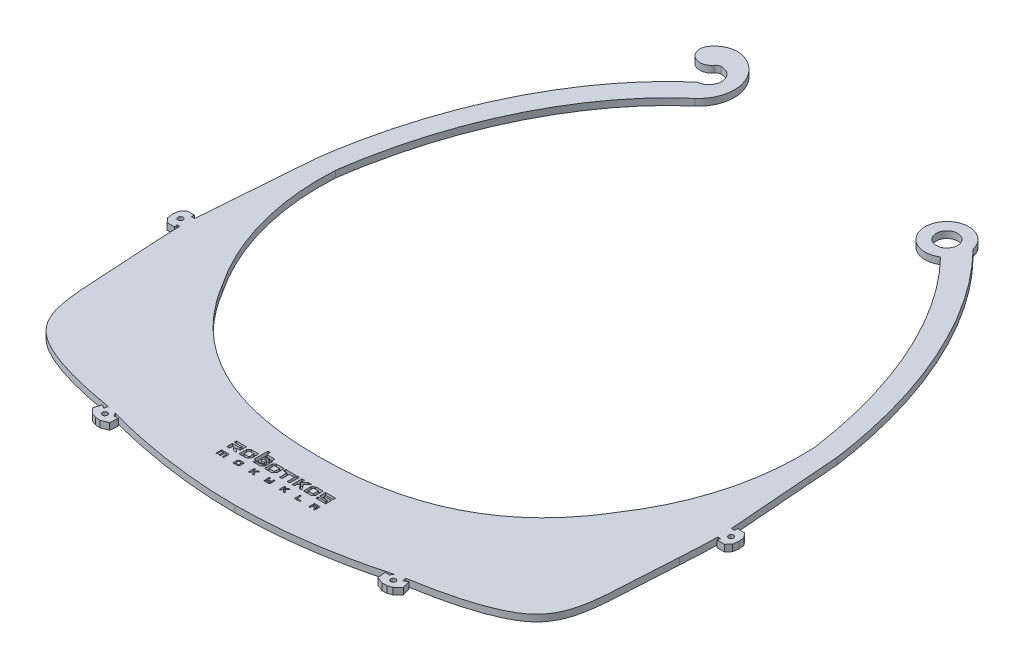
SolidWorks part; units mm, degrees
ref_plane "Front Plane" through (0, 0, 0) normal (0, 0, 1) x (1, 0, 0)
ref_plane "Top Plane" through (0, 0, 0) normal (0, 1, 0) x (1, 0, 0)
ref_plane "Right Plane" through (0, 0, 0) normal (1, 0, 0) x (0, 0, -1)
sketch "Sketch1" plane through (0, 0, 0) normal (0, 1, 0) x (1, 0, 0)
  line L0 (-56.7342, 4649.685) -> (-54.3432, 4649.8666)
  line L1 (-54.3432, 4649.8666) -> (-51.9673, 4650.1279)
  line L2 (-51.9673, 4650.1279) -> (-49.6128, 4650.4904)
  line L3 (-49.6128, 4650.4904) -> (-47.2873, 4650.9763)
  line L4 (-47.2873, 4650.9763) -> (-45.0028, 4651.606)
  line L5 (-45.0028, 4651.606) -> (-42.7754, 4652.393)
  line L6 (-42.7754, 4652.393) -> (-40.6236, 4653.3398)
  line L7 (-40.6236, 4653.3398) -> (-38.5569, 4654.4471)
  line L8 (-38.5569, 4654.4471) -> (-36.5628, 4655.7048)
  line L9 (-36.5628, 4655.7048) -> (-34.628, 4657.0886)
  line L10 (-34.628, 4657.0886) -> (-32.7572, 4658.5809)
  line L11 (-32.7572, 4658.5809) -> (-31.8781, 4659.3559)
  line L12 (-31.8781, 4659.3559) -> (-31.0378, 4660.1663)
  line L13 (-31.0378, 4660.1663) -> (-30.2434, 4661.0133)
  line L14 (-30.2434, 4661.0133) -> (-29.4929, 4661.8977)
  line L15 (-29.4929, 4661.8977) -> (-28.0377, 4663.8002)
  line L16 (-28.0377, 4663.8002) -> (-26.6418, 4665.7643)
  line L17 (-26.6418, 4665.7643) -> (-25.2842, 4667.7433)
  line L18 (-25.2842, 4667.7433) -> (-24.5616, 4668.7671)
  line L19 (-24.5616, 4668.7671) -> (-24.1207, 4669.3049)
  line L20 (-24.1207, 4669.3049) -> (-23.6287, 4669.8041)
  line L21 (-23.6287, 4669.8041) -> (-22.6527, 4670.6453)
  line L22 (-22.6527, 4670.6453) -> (-21.6624, 4671.4168)
  line L23 (-21.6624, 4671.4168) -> (-19.7154, 4672.8766)
  line L24 (-19.7154, 4672.8766) -> (-18.7888, 4673.6051)
  line L25 (-18.7888, 4673.6051) -> (-17.9151, 4674.3646)
  line L26 (-17.9151, 4674.3646) -> (-17.0961, 4675.1711)
  line L27 (-17.0961, 4675.1711) -> (-16.3332, 4676.0235)
  line L28 (-16.3332, 4676.0235) -> (-14.888, 4677.8872)
  line L29 (-14.888, 4677.8872) -> (-14.2651, 4678.8282)
  line L30 (-14.2651, 4678.8282) -> (-13.7395, 4679.8092)
  line L31 (-13.7395, 4679.8092) -> (-13.3157, 4680.8364)
  line L32 (-13.3157, 4680.8364) -> (-12.9921, 4681.9053)
  line L33 (-12.9921, 4681.9053) -> (-12.765, 4683.0137)
  line L34 (-12.765, 4683.0137) -> (-12.6116, 4684.156)
  line L35 (-12.6116, 4684.156) -> (-12.4221, 4686.5439)
  line L36 (-12.4221, 4686.5439) -> (-12.3049, 4688.9547)
  line L37 (-12.3049, 4688.9547) -> (-12.23, 4691.3606)
  line L38 (-12.23, 4691.3606) -> (-12.2173, 4693.7469)
  line L39 (-12.2173, 4693.7469) -> (-12.2979, 4696.128)
  line L40 (-12.2979, 4696.128) -> (-12.4621, 4698.525)
  line L41 (-12.4621, 4698.525) -> (-12.9016, 4703.3562)
  line L42 (-12.9016, 4703.3562) -> (-13.1725, 4705.7323)
  line L43 (-13.1725, 4705.7323) -> (-13.359, 4706.8497)
  line L44 (-13.359, 4706.8497) -> (-13.6464, 4707.8976)
  line L45 (-13.6464, 4707.8976) -> (-13.8331, 4708.3435)
  line L46 (-13.8331, 4708.3435) -> (-14.0727, 4708.7863)
  line L47 (-14.0727, 4708.7863) -> (-14.3603, 4709.2104)
  line L48 (-14.3603, 4709.2104) -> (-14.6922, 4709.6118)
  line L49 (-14.6922, 4709.6118) -> (-15.5352, 4710.4427)
  line L50 (-15.5352, 4710.4427) -> (-16.4733, 4711.2489)
  line L51 (-16.4733, 4711.2489) -> (-18.3969, 4712.8768)
  line L52 (-18.3969, 4712.8768) -> (-19.3317, 4713.7593)
  line L53 (-19.3317, 4713.7593) -> (-19.7964, 4714.2738)
  line L54 (-19.7964, 4714.2738) -> (-20.226, 4714.8564)
  line L55 (-20.226, 4714.8564) -> (-20.8491, 4716.0227)
  line L56 (-20.8491, 4716.0227) -> (-21.3607, 4717.2182)
  line L57 (-21.3607, 4717.2182) -> (-22.2565, 4719.6128)
  line L58 (-22.2565, 4719.6128) -> (-23.9365, 4724.4003)
  line L59 (-23.9365, 4724.4003) -> (-24.8142, 4726.6925)
  line L60 (-24.8142, 4726.6925) -> (-25.7235, 4728.951)
  line L61 (-25.7235, 4728.951) -> (-29.4192, 4737.978)
  line L62 (-29.4192, 4737.978) -> (-31.3112, 4742.476)
  line L63 (-31.3112, 4742.476) -> (-32.3108, 4744.6883)
  line L64 (-32.3108, 4744.6883) -> (-33.3653, 4746.8748)
  line L65 (-33.3653, 4746.8748) -> (-34.484, 4749.0197)
  line L66 (-34.484, 4749.0197) -> (-35.6822, 4751.1089)
  line L67 (-35.6822, 4751.1089) -> (-36.9697, 4753.1376)
  line L68 (-36.9697, 4753.1376) -> (-38.335, 4755.1176)
  line L69 (-38.335, 4755.1176) -> (-39.7566, 4757.0561)
  line L70 (-39.7566, 4757.0561) -> (-41.2239, 4758.9538)
  line L71 (-41.2239, 4758.9538) -> (-44.2837, 4762.6862)
  line L72 (-44.2837, 4762.6862) -> (-45.0093, 4763.5782)
  line L73 (-45.7102, 4766.0333) -> (-45.6003, 4766.895)
  line L74 (-44.3387, 4767.2717) -> (-41.5099, 4763.9631)
  line L75 (-41.5099, 4763.9631) -> (-39.7615, 4761.7893)
  line L76 (-39.7615, 4761.7893) -> (-36.1552, 4757.1077)
  line L77 (-36.1552, 4757.1077) -> (-34.4224, 4754.6956)
  line L78 (-34.4224, 4754.6956) -> (-32.818, 4752.1875)
  line L79 (-32.818, 4752.1875) -> (-31.4001, 4749.5854)
  line L80 (-31.4001, 4749.5854) -> (-30.1172, 4746.945)
  line L81 (-30.1172, 4746.945) -> (-27.7453, 4741.6402)
  line L82 (-27.7453, 4741.6402) -> (-25.4835, 4736.2816)
  line L83 (-25.4835, 4736.2816) -> (-23.2904, 4730.8724)
  line L84 (-23.2904, 4730.8724) -> (-21.1708, 4725.4153)
  line L85 (-21.1708, 4725.4153) -> (-19.1018, 4719.943)
  line L86 (-19.1018, 4719.943) -> (-18.1004, 4717.2034)
  line L87 (-18.1004, 4717.2034) -> (-17.875, 4716.5966)
  line L88 (-17.875, 4716.5966) -> (-17.6236, 4716.1359)
  line L89 (-17.6236, 4716.1359) -> (-17.2675, 4715.7336)
  line L90 (-17.2675, 4715.7336) -> (-16.7845, 4715.2999)
  line L91 (-16.7845, 4715.2999) -> (-14.566, 4713.4273)
  line L92 (-14.566, 4713.4273) -> (-13.4359, 4712.453)
  line L93 (-13.4359, 4712.453) -> (-12.2875, 4711.3506)
  line L94 (-12.2875, 4711.3506) -> (-11.7288, 4710.5494)
  line L95 (-11.7288, 4710.5494) -> (-11.4049, 4709.6505)
  line L96 (-11.4049, 4709.6505) -> (-11.1035, 4708.0976)
  line L97 (-11.1035, 4708.0976) -> (-10.7039, 4705.1867)
  line L98 (-10.7039, 4705.1867) -> (-10.3782, 4702.2301)
  line L99 (-10.3782, 4702.2301) -> (-10.1381, 4699.312)
  line L100 (-10.1381, 4699.312) -> (-9.9526, 4696.4059)
  line L101 (-9.9526, 4696.4059) -> (-9.8234, 4693.4642)
  line L102 (-9.8234, 4693.4642) -> (-9.7818, 4690.5097)
  line L103 (-9.7818, 4690.5097) -> (-9.8395, 4687.5651)
  line L104 (-9.8395, 4687.5651) -> (-10.1467, 4681.8499)
  line L105 (-10.2187, 4680.4106) -> (-10.5778, 4674.8324)
  line L106 (-10.5778, 4674.8324) -> (-10.9255, 4669.1921)
  line L107 (-10.9255, 4669.1921) -> (-11.1085, 4666.3239)
  line L108 (-11.1085, 4666.3239) -> (-11.3672, 4663.3976)
  line L109 (-11.3672, 4663.3976) -> (-11.5954, 4661.8877)
  line L110 (-11.5954, 4661.8877) -> (-11.9481, 4660.3817)
  line L111 (-11.9481, 4660.3817) -> (-12.469, 4658.9063)
  line L112 (-12.469, 4658.9063) -> (-13.1768, 4657.5086)
  line L113 (-13.1768, 4657.5086) -> (-14.0475, 4656.2056)
  line L114 (-14.0475, 4656.2056) -> (-15.0678, 4655.0233)
  line L115 (-15.0678, 4655.0233) -> (-15.6664, 4654.4674)
  line L116 (-15.6664, 4654.4674) -> (-16.3022, 4653.9611)
  line L117 (-16.3022, 4653.9611) -> (-17.6055, 4653.1269)
  line L118 (-17.6055, 4653.1269) -> (-18.9712, 4652.4383)
  line L119 (-18.9712, 4652.4383) -> (-20.3502, 4651.8561)
  line L120 (-20.3502, 4651.8561) -> (-21.7405, 4651.3486)
  line L121 (-21.7405, 4651.3486) -> (-23.1491, 4650.8937)
  line L122 (-23.1491, 4650.8937) -> (-25.9685, 4650.1281)
  line L123 (-25.9685, 4650.1281) -> (-28.8127, 4649.495)
  line L124 (-28.8127, 4649.495) -> (-34.3611, 4648.4388)
  line L125 (-35.7786, 4648.1905) -> (-42.1243, 4647.1501)
  line L126 (-42.1243, 4647.1501) -> (-45.3893, 4646.7207)
  line L127 (-45.3893, 4646.7207) -> (-48.6635, 4646.3827)
  line L128 (-48.6635, 4646.3827) -> (-55.1892, 4645.922)
  line L129 (-55.1892, 4645.922) -> (-61.7354, 4645.5886)
  line L130 (-61.7354, 4645.5886) -> (-63.9666, 4645.5453)
  line L131 (-63.9667, 4649.4865) -> (-59.1315, 4649.5688)
  line L132 (-59.1315, 4649.5688) -> (-56.7342, 4649.685)
  line L133 (-9.7721, 4681.8294) -> (-9.752, 4682.186)
  line L134 (-9.752, 4682.186) -> (-9.3693, 4682.5229)
  line L135 (-9.3693, 4682.5229) -> (-8.649, 4682.4768)
  line L136 (-8.649, 4682.4768) -> (-7.9775, 4681.713)
  line L137 (-7.9775, 4681.713) -> (-8.2411, 4680.2884)
  line L138 (-8.2411, 4680.2884) -> (-9.0059, 4679.6162)
  line L139 (-9.0059, 4679.6162) -> (-9.5491, 4679.6473)
  line L140 (-9.5491, 4679.6473) -> (-9.8867, 4680.0303)
  line L141 (-9.8867, 4680.0303) -> (-9.8664, 4680.3889)
  line L142 (-9.7721, 4681.8294) -> (-9.752, 4682.186)
  line L151 (-34.2991, 4648.0806) -> (-33.9447, 4648.1421)
  line L152 (-33.9447, 4648.1421) -> (-33.5285, 4647.8485)
  line L153 (-33.5285, 4647.8485) -> (-33.4056, 4647.1395)
  line L154 (-33.4056, 4647.1395) -> (-33.9931, 4646.3074)
  line L155 (-33.9931, 4646.3074) -> (-35.4108, 4646.0612)
  line L156 (-35.4108, 4646.0612) -> (-36.2441, 4646.6493)
  line L157 (-36.2441, 4646.6493) -> (-36.3669, 4647.358)
  line L158 (-36.3669, 4647.358) -> (-36.0733, 4647.7743)
  line L159 (-36.0733, 4647.7743) -> (-35.7187, 4647.8357)
  line L160 (-10.1467, 4681.8499) -> (-9.7721, 4681.8294)
  line L161 (-34.3611, 4648.4388) -> (-34.2991, 4648.0806)
  line L162 (-35.7786, 4648.1905) -> (-35.7187, 4647.8357)
  line L163 (-9.8664, 4680.3889) -> (-10.2187, 4680.4106)
  line L165 (-118.1813, 4682.186) -> (-118.5641, 4682.5226)
  line L166 (-118.5641, 4682.5226) -> (-119.2843, 4682.4768)
  line L167 (-119.2843, 4682.4768) -> (-119.9558, 4681.7128)
  line L168 (-119.9558, 4681.7128) -> (-119.8643, 4680.2786)
  line L169 (-119.8643, 4680.2786) -> (-119.0995, 4679.6064)
  line L170 (-119.0995, 4679.6064) -> (-118.3843, 4679.6471)
  line L171 (-118.3843, 4679.6471) -> (-118.0466, 4680.0303)
  line L172 (-118.0466, 4680.0303) -> (-118.0672, 4680.3889)
  line L173 (-118.0672, 4680.3889) -> (-117.7148, 4680.4103)
  line L174 (-117.7148, 4680.4103) -> (-117.3555, 4674.8322)
  line L175 (-117.3555, 4674.8322) -> (-117.0078, 4669.1921)
  line L176 (-117.0078, 4669.1921) -> (-116.8249, 4666.3237)
  line L177 (-116.8249, 4666.3237) -> (-116.566, 4663.3974)
  line L178 (-116.566, 4663.3974) -> (-116.3378, 4661.8875)
  line L179 (-116.3378, 4661.8875) -> (-115.9851, 4660.3817)
  line L180 (-115.9851, 4660.3817) -> (-115.4645, 4658.906)
  line L181 (-115.4645, 4658.906) -> (-114.7563, 4657.5086)
  line L182 (-114.7563, 4657.5086) -> (-113.8857, 4656.2053)
  line L183 (-113.8857, 4656.2053) -> (-112.8656, 4655.0233)
  line L184 (-112.8656, 4655.0233) -> (-112.2669, 4654.4674)
  line L185 (-112.2669, 4654.4674) -> (-111.6311, 4653.9608)
  line L186 (-111.6311, 4653.9608) -> (-110.328, 4653.1269)
  line L187 (-110.328, 4653.1269) -> (-108.9621, 4652.4383)
  line L188 (-108.9621, 4652.4383) -> (-107.5832, 4651.8561)
  line L189 (-107.5832, 4651.8561) -> (-106.1928, 4651.3484)
  line L190 (-106.1928, 4651.3484) -> (-104.7844, 4650.8937)
  line L191 (-104.7844, 4650.8937) -> (-101.9649, 4650.1279)
  line L192 (-101.9649, 4650.1279) -> (-99.1205, 4649.4948)
  line L193 (-99.1205, 4649.4948) -> (-93.5721, 4648.4388)
  line L194 (-93.5721, 4648.4388) -> (-93.6341, 4648.0806)
  line L195 (-93.6341, 4648.0806) -> (-93.9885, 4648.1421)
  line L196 (-93.9885, 4648.1421) -> (-94.4046, 4647.8485)
  line L197 (-94.4046, 4647.8485) -> (-94.5276, 4647.1392)
  line L198 (-94.5276, 4647.1392) -> (-93.9404, 4646.3074)
  line L199 (-93.9404, 4646.3074) -> (-92.5223, 4646.0612)
  line L200 (-92.5223, 4646.0612) -> (-91.6891, 4646.6493)
  line L201 (-91.6891, 4646.6493) -> (-91.5662, 4647.358)
  line L202 (-91.5662, 4647.358) -> (-91.8598, 4647.7743)
  line L203 (-91.8598, 4647.7743) -> (-92.2145, 4647.8357)
  line L204 (-92.1546, 4648.1905) -> (-92.2145, 4647.8357)
  line L205 (-92.1546, 4648.1905) -> (-85.8089, 4647.1501)
  line L206 (-85.8089, 4647.1501) -> (-82.5441, 4646.7204)
  line L207 (-82.5441, 4646.7204) -> (-79.2698, 4646.3827)
  line L208 (-79.2698, 4646.3827) -> (-72.7439, 4645.922)
  line L209 (-72.7439, 4645.922) -> (-66.1978, 4645.5886)
  line L210 (-66.1978, 4645.5886) -> (-63.9666, 4645.5453)
  line L211 (-63.9667, 4649.4865) -> (-68.8018, 4649.5688)
  line L212 (-68.8018, 4649.5688) -> (-71.1991, 4649.685)
  line L213 (-71.1991, 4649.685) -> (-73.5901, 4649.8666)
  line L214 (-73.5901, 4649.8666) -> (-75.9659, 4650.1279)
  line L215 (-75.9659, 4650.1279) -> (-78.3204, 4650.4904)
  line L216 (-78.3204, 4650.4904) -> (-80.646, 4650.976)
  line L217 (-80.646, 4650.976) -> (-82.9304, 4651.606)
  line L218 (-82.9304, 4651.606) -> (-85.1578, 4652.393)
  line L219 (-85.1578, 4652.393) -> (-87.3097, 4653.3398)
  line L220 (-87.3097, 4653.3398) -> (-89.3762, 4654.4469)
  line L221 (-89.3762, 4654.4469) -> (-91.3704, 4655.7045)
  line L222 (-91.3704, 4655.7045) -> (-93.3054, 4657.0883)
  line L223 (-93.3054, 4657.0883) -> (-95.1761, 4658.5809)
  line L224 (-95.1761, 4658.5809) -> (-96.0551, 4659.3559)
  line L225 (-96.0551, 4659.3559) -> (-96.8955, 4660.1661)
  line L226 (-96.8955, 4660.1661) -> (-97.6899, 4661.013)
  line L227 (-97.6899, 4661.013) -> (-98.4405, 4661.8974)
  line L228 (-98.4405, 4661.8974) -> (-99.8956, 4663.8003)
  line L229 (-99.8956, 4663.8003) -> (-101.2917, 4665.7643)
  line L230 (-101.2917, 4665.7643) -> (-102.649, 4667.7433)
  line L231 (-102.649, 4667.7433) -> (-103.3717, 4668.7671)
  line L232 (-103.3717, 4668.7671) -> (-103.8126, 4669.3049)
  line L233 (-103.8126, 4669.3049) -> (-104.3045, 4669.8038)
  line L234 (-104.3045, 4669.8038) -> (-105.2805, 4670.645)
  line L235 (-105.2805, 4670.645) -> (-106.2711, 4671.4168)
  line L236 (-106.2711, 4671.4168) -> (-108.218, 4672.8766)
  line L237 (-108.218, 4672.8766) -> (-109.1446, 4673.6051)
  line L238 (-109.1446, 4673.6051) -> (-110.0184, 4674.3646)
  line L239 (-110.0184, 4674.3646) -> (-110.8371, 4675.1711)
  line L240 (-110.8371, 4675.1711) -> (-111.6001, 4676.0232)
  line L241 (-111.6001, 4676.0232) -> (-113.0454, 4677.8872)
  line L242 (-113.0454, 4677.8872) -> (-113.6683, 4678.8282)
  line L243 (-113.6683, 4678.8282) -> (-114.1938, 4679.8092)
  line L244 (-114.1938, 4679.8092) -> (-114.6176, 4680.8364)
  line L245 (-114.6176, 4680.8364) -> (-114.9413, 4681.905)
  line L246 (-114.9413, 4681.905) -> (-115.1684, 4683.0135)
  line L247 (-115.1684, 4683.0135) -> (-115.3218, 4684.156)
  line L248 (-115.3218, 4684.156) -> (-115.5115, 4686.5436)
  line L249 (-115.5115, 4686.5436) -> (-115.6283, 4688.9545)
  line L250 (-115.6283, 4688.9545) -> (-115.7033, 4691.3606)
  line L251 (-115.7033, 4691.3606) -> (-115.7161, 4693.7466)
  line L252 (-115.7161, 4693.7466) -> (-115.6355, 4696.1278)
  line L253 (-115.6355, 4696.1278) -> (-115.4714, 4698.525)
  line L254 (-115.4714, 4698.525) -> (-115.0316, 4703.3562)
  line L255 (-115.0316, 4703.3562) -> (-114.7608, 4705.732)
  line L256 (-114.7608, 4705.732) -> (-114.5743, 4706.8497)
  line L257 (-114.5743, 4706.8497) -> (-114.287, 4707.8977)
  line L258 (-114.287, 4707.8977) -> (-114.1002, 4708.3435)
  line L259 (-114.1002, 4708.3435) -> (-113.8608, 4708.7862)
  line L260 (-113.8608, 4708.7862) -> (-113.5731, 4709.2103)
  line L261 (-113.5731, 4709.2103) -> (-113.2411, 4709.6117)
  line L262 (-113.2411, 4709.6117) -> (-112.3981, 4710.4425)
  line L263 (-112.3981, 4710.4425) -> (-111.4599, 4711.2487)
  line L264 (-111.4599, 4711.2487) -> (-109.5364, 4712.8767)
  line L265 (-109.5364, 4712.8767) -> (-108.602, 4713.7592)
  line L266 (-108.602, 4713.7592) -> (-108.1369, 4714.2737)
  line L267 (-108.1369, 4714.2737) -> (-107.7072, 4714.8564)
  line L268 (-107.7072, 4714.8564) -> (-107.0842, 4716.0225)
  line L269 (-107.0842, 4716.0225) -> (-106.5727, 4717.2181)
  line L270 (-106.5727, 4717.2181) -> (-105.6769, 4719.6127)
  line L271 (-105.6769, 4719.6127) -> (-103.9969, 4724.4001)
  line L272 (-103.9969, 4724.4001) -> (-103.1193, 4726.6924)
  line L273 (-103.1193, 4726.6924) -> (-102.2099, 4728.9509)
  line L274 (-102.2099, 4728.9509) -> (-98.5143, 4737.9778)
  line L275 (-98.5143, 4737.9778) -> (-96.6221, 4742.4757)
  line L276 (-96.6221, 4742.4757) -> (-95.6227, 4744.6884)
  line L277 (-95.6227, 4744.6884) -> (-94.5682, 4746.8748)
  line L278 (-94.5682, 4746.8748) -> (-93.4493, 4749.0197)
  line L279 (-93.4493, 4749.0197) -> (-92.2515, 4751.1088)
  line L280 (-92.2515, 4751.1088) -> (-90.9637, 4753.1374)
  line L281 (-90.9637, 4753.1374) -> (-89.5985, 4755.1174)
  line L282 (-89.5985, 4755.1174) -> (-88.177, 4757.0561)
  line L283 (-88.177, 4757.0561) -> (-86.7094, 4758.9538)
  line L284 (-86.7094, 4758.9538) -> (-83.65, 4762.6862)
  line L285 (-83.65, 4762.6862) -> (-82.924, 4763.5782)
  line L286 (-82.2232, 4766.0334) -> (-82.3333, 4766.8949)
  line L287 (-83.5948, 4767.2716) -> (-86.4235, 4763.963)
  line L288 (-86.4235, 4763.963) -> (-88.172, 4761.7894)
  line L289 (-88.172, 4761.7894) -> (-91.7784, 4757.1074)
  line L290 (-91.7784, 4757.1074) -> (-93.5112, 4754.6958)
  line L291 (-93.5112, 4754.6958) -> (-95.1154, 4752.1875)
  line L292 (-95.1154, 4752.1875) -> (-96.5333, 4749.5852)
  line L293 (-96.5333, 4749.5852) -> (-97.8162, 4746.9449)
  line L294 (-97.8162, 4746.9449) -> (-100.1881, 4741.6403)
  line L295 (-100.1881, 4741.6403) -> (-102.4501, 4736.2814)
  line L296 (-102.4501, 4736.2814) -> (-104.6429, 4730.8726)
  line L297 (-104.6429, 4730.8726) -> (-106.7626, 4725.415)
  line L298 (-106.7626, 4725.415) -> (-108.8314, 4719.9429)
  line L299 (-108.8314, 4719.9429) -> (-109.8329, 4717.2035)
  line L300 (-109.8329, 4717.2035) -> (-110.0583, 4716.5964)
  line L301 (-110.0583, 4716.5964) -> (-110.3097, 4716.1357)
  line L302 (-110.3097, 4716.1357) -> (-110.6661, 4715.7335)
  line L303 (-110.6661, 4715.7335) -> (-111.1489, 4715.2998)
  line L304 (-111.1489, 4715.2998) -> (-113.3676, 4713.4272)
  line L305 (-113.3676, 4713.4272) -> (-114.4976, 4712.4528)
  line L306 (-114.4976, 4712.4528) -> (-115.646, 4711.3505)
  line L307 (-115.646, 4711.3505) -> (-116.2044, 4710.5493)
  line L308 (-116.2044, 4710.5493) -> (-116.5286, 4709.6504)
  line L309 (-116.5286, 4709.6504) -> (-116.8298, 4708.0975)
  line L310 (-116.8298, 4708.0975) -> (-117.2296, 4705.1868)
  line L311 (-117.2296, 4705.1868) -> (-117.5553, 4702.2301)
  line L312 (-117.5553, 4702.2301) -> (-117.7952, 4699.312)
  line L313 (-117.7952, 4699.312) -> (-117.981, 4696.4059)
  line L314 (-117.981, 4696.4059) -> (-118.11, 4693.4642)
  line L315 (-118.11, 4693.4642) -> (-118.1516, 4690.5097)
  line L316 (-118.1516, 4690.5097) -> (-118.0939, 4687.5649)
  line L317 (-118.0939, 4687.5649) -> (-117.7865, 4681.8497)
  line L318 (-117.7865, 4681.8497) -> (-118.1612, 4681.8294)
  line L319 (-118.1612, 4681.8294) -> (-118.1813, 4682.186)
  spline S0 degree 3 poles (-45.7102, 4766.0333) (-45.8224, 4765.1537) (-45.5692, 4764.2663) (-45.0093, 4763.5782) knots 0 0 0 0 1 1 1 1
  spline S1 degree 3 poles (-44.3387, 4767.2717) (-44.5973, 4767.574) (-45.0517, 4767.6095) (-45.3539, 4767.351) knots 0 0 0 0 1 1 1 1
  spline S2 degree 3 poles (-45.3539, 4767.351) (-45.4898, 4767.2349) (-45.5777, 4767.0723) (-45.6003, 4766.895) knots 0 0 0 0 1 1 1 1
  spline S3 degree 3 poles (-82.924, 4763.5782) (-82.3642, 4764.2661) (-82.111, 4765.1536) (-82.2232, 4766.0334) knots 0 0 0 0 1 1 1 1
  spline S4 degree 3 poles (-82.3333, 4766.8949) (-82.3835, 4767.2894) (-82.7441, 4767.5683) (-83.1386, 4767.518) knots 0 0 0 0 1 1 1 1
  spline S5 degree 3 poles (-83.1386, 4767.518) (-83.3159, 4767.4954) (-83.4785, 4767.4075) (-83.5948, 4767.2716) knots 0 0 0 0 1 1 1 1
sketch "Sketch2" plane through (0, 0, 0) normal (0, 1, 0) x (1, 0, 0)
  line L32 (-22.4985, 4637.3551) -> (-19.7034, 4638.0357) construction
  line L49 (-146.8202, 4697.6298) -> (-149.3915, 4697.5949) construction
  line L55 (-21.481, 4637.6954) -> (-21.0917, 4635.6618) construction
  line L62 (-144.7504, 4697.658) -> (-146.8202, 4697.6298) construction
  line L98 (-64.3034, 4656.5726) -> (-64.3034, 4631.4262) construction
  line L99 (-107.5151, 4635.6618) -> (-108, 4633.1287) construction
  line L100 (-107.1258, 4637.6954) -> (-107.5151, 4635.6618) construction
  line L101 (-106.1083, 4637.3551) -> (-108.9034, 4638.0357) construction
  line L102 (-145.774, 4699.7908) -> (-145.6794, 4700.6671)
  line L103 (-144.7504, 4699.7908) -> (-145.774, 4699.7908)
  line L104 (-145.7738, 4695.5191) -> (-145.5973, 4694.6247)
  line L105 (-144.9397, 4695.5191) -> (-145.7738, 4695.5191)
  line L106 (-109.111, 4636.9369) -> (-108.9034, 4638.0357)
  line L107 (-110.2284, 4637.6126) -> (-109.111, 4636.9369)
  line L108 (-105.5775, 4636.4725) -> (-106.1083, 4637.3551)
  line L109 (-104.2732, 4636.4725) -> (-105.5775, 4636.4725)
  line L112 (-110.2284, 4637.6126) -> (-110.9044, 4635.297)
  line L113 (-104.2732, 4636.4725) -> (-104.5002, 4634.071)
  line L114 (-145.5973, 4694.6247) -> (-147.8371, 4694.6247)
  line L115 (-145.6794, 4700.6671) -> (-147.9184, 4700.6062)
  line L116 (-147.8371, 4694.6247) -> (-148.983, 4695.9445)
  line L117 (-148.983, 4695.9445) -> (-149.2228, 4697.5972)
  line L118 (-149.028, 4699.2558) -> (-149.2228, 4697.5972)
  line L119 (-147.9184, 4700.6062) -> (-149.028, 4699.2558)
  line L120 (-104.5002, 4634.071) -> (-106.5343, 4633.2642)
  line L121 (-106.5343, 4633.2642) -> (-107.9595, 4633.3404)
  line L122 (-109.3121, 4633.796) -> (-107.9595, 4633.3404)
  line L123 (-110.9044, 4635.297) -> (-109.3121, 4633.796)
  line L146 (-64.3034, 4656.5726) -> (-64.3034, 4858.4357) construction
  line L147 (-21.0917, 4635.6618) -> (-20.6068, 4633.1287) construction
  line L148 (16.1436, 4697.658) -> (18.2134, 4697.6298) construction
  line L149 (18.2134, 4697.6298) -> (20.7848, 4697.5949) construction
  line L150 (-17.7023, 4635.297) -> (-19.2947, 4633.796)
  line L151 (-19.2947, 4633.796) -> (-20.6473, 4633.3404)
  line L152 (-22.0725, 4633.2642) -> (-20.6473, 4633.3404)
  line L153 (-24.1066, 4634.071) -> (-22.0725, 4633.2642)
  line L154 (19.3116, 4700.6062) -> (20.4212, 4699.2558)
  line L155 (20.4212, 4699.2558) -> (20.616, 4697.5972)
  line L156 (20.3762, 4695.9445) -> (20.616, 4697.5972)
  line L157 (19.2303, 4694.6247) -> (20.3762, 4695.9445)
  line L158 (17.0726, 4700.6671) -> (19.3116, 4700.6062)
  line L159 (16.9905, 4694.6247) -> (19.2303, 4694.6247)
  line L160 (-24.3336, 4636.4725) -> (-24.1066, 4634.071)
  line L161 (-18.3784, 4637.6126) -> (-17.7023, 4635.297)
  line L162 (-24.3336, 4636.4725) -> (-23.0292, 4636.4725)
  line L163 (-23.0292, 4636.4725) -> (-22.4985, 4637.3551)
  line L164 (-18.3784, 4637.6126) -> (-19.4958, 4636.9369)
  line L165 (-19.4958, 4636.9369) -> (-19.7034, 4638.0357)
  line L166 (16.333, 4695.5191) -> (17.167, 4695.5191)
  line L167 (17.167, 4695.5191) -> (16.9905, 4694.6247)
  line L168 (16.1436, 4699.7908) -> (17.1672, 4699.7908)
  line L169 (17.1672, 4699.7908) -> (17.0726, 4700.6671)
  line L171 (-144.7504, 4699.7908) -> (-142.1125, 4734.0467)
  line L172 (13.5057, 4734.0467) -> (16.1436, 4699.7908)
  circle A10 centre (-146.8202, 4697.6298) radius 0.75
  circle A11 centre (-107.5151, 4635.6618) radius 0.75
  arc A20 (-123.3137, 4686.6697) -> (-136.138, 4733.4486) centre (-60.9323, 4728.9186) cw
  arc A42 (-100.9639, 4805.9508) -> (-104.2247, 4824.0438) centre (-107.9207, 4814.0373) ccw
  arc A43 (-128.2816, 4683.3051) -> (-142.1125, 4734.0467) centre (-60.9323, 4728.9186) cw construction
  arc A47 (-104.2247, 4824.0438) -> (-112.368, 4821.5982) centre (-106.673, 4817.4154) ccw
  arc A48 (-112.368, 4821.5982) -> (-106.673, 4817.4154) centre (-109.5205, 4819.5068) ccw
  arc A49 (-106.673, 4817.4154) -> (-105.3758, 4818.1262) centre (-105.2615, 4816.3786) cw
  arc A50 (-105.3758, 4818.1262) -> (-104.8769, 4810.4992) centre (-105.1263, 4814.3127) cw
  arc A56 (-5.293, 4686.6697) -> (7.5312, 4733.4486) centre (-67.6745, 4728.9186) ccw
  circle A58 centre (-21.0917, 4635.6618) radius 0.75
  circle A59 centre (18.2134, 4697.6298) radius 0.75
  circle A60 centre (-26.5764, 4807.1146) radius 3.1698
  arc A62 (-20.1404, 4808.5054) -> (-22.9892, 4801.5929) centre (-26.5764, 4807.1146) ccw
  ellipse E0 centre (-64.3034, 4711.1528) end of major axis (-64.3034, 4601.7157) minor radius 73.3735 (-100.9639, 4805.9508) -> (-136.138, 4733.4486) ccw
  ellipse E1 centre (-64.3034, 4711.1528) end of major axis (-64.3034, 4601.7157) minor radius 73.3735 (-22.9892, 4801.5929) -> (7.5312, 4733.4486) cw
  spline S0 degree 1 poles (-104.8769, 4810.4992) (-142.1125, 4734.0467) knots 0 0 1 1 construction
  spline S1 degree 3 poles (-104.8769, 4810.4992) (-106.0966, 4809.4499) (-108.4586, 4807.2909) (-113.0376, 4802.5955) (-118.39, 4796.1155) (-124.19, 4787.4329) (-129.3119, 4777.9468) (-133.7143, 4767.7579) (-137.3584, 4756.9759) (-139.7372, 4747.5879) (-141.2318, 4739.9021) (-141.843, 4735.9987) (-142.1125, 4734.0467) knots -2.618407 -2.618407 -2.618407 -2.618407 -2.565625 -2.512842 -2.407277 -2.301712 -2.196147 -2.090582 -1.985018 -1.879453 -1.82667 -1.773888 -1.773888 -1.773888 -1.773888
  spline S2 degree 3 poles (-64.3034, 4631.4262) (-50.3772, 4631.4534) (-36.075, 4633.5591) (-22.4985, 4637.3551) knots 0.500293 0.500293 0.500293 0.500293 0.981945 0.981945 0.981945 0.981945
  spline S3 degree 3 poles (-19.7034, 4638.0357) (-9.7848, 4639.6859) (3.8867, 4643.0604) (15.612, 4654.3944) (14.4923, 4666.3346) (15.8572, 4684.5147) knots 0.018902 0.018902 0.018902 0.018902 0.394122 0.490995 0.987629 0.987629 0.987629 0.987629
  spline S4 degree 3 poles (15.8572, 4684.5147) (15.9993, 4687.5885) (16.2951, 4691.3248) (16.333, 4695.5191) knots 0.004735 0.004735 0.004735 0.004735 0.035162 0.035162 0.035162 0.035162
  spline S5 degree 2 poles (-64.3034, 4656.5726) (-23.4234, 4656.2934) (-5.293, 4686.6697) knots 0 0 0 1 1 1
  spline S6 degree 3 poles (-20.1404, 4808.5054) (-19.3392, 4807.6988) (-16.1692, 4804.3852) (-10.9594, 4798.0733) (-4.9374, 4789.0491) (0.3595, 4779.2259) (4.8966, 4768.7067) (8.6413, 4757.6016) (11.0788, 4747.9502) (12.6072, 4740.0563) (13.2309, 4736.0503) (13.5057, 4734.0467) knots -2.547822 -2.547822 -2.547822 -2.547822 -2.512682 -2.406957 -2.301232 -2.195507 -2.089782 -1.984057 -1.878332 -1.825469 -1.772607 -1.772607 -1.772607 -1.772607
  spline S15 degree 2 poles (-64.3034, 4656.5726) (-105.1833, 4656.2934) (-123.3137, 4686.6697) knots 0 0 0 1 1 1
  spline S19 degree 3 poles (-144.464, 4684.5147) (-144.6061, 4687.5885) (-144.9019, 4691.3248) (-144.9397, 4695.5191) knots 0.004735 0.004735 0.004735 0.004735 0.035162 0.035162 0.035162 0.035162
  spline S20 degree 3 poles (-108.9034, 4638.0357) (-118.822, 4639.6859) (-132.4935, 4643.0604) (-144.2188, 4654.3944) (-143.0991, 4666.3346) (-144.464, 4684.5147) knots 0.018902 0.018902 0.018902 0.018902 0.394122 0.490995 0.987629 0.987629 0.987629 0.987629
  spline S21 degree 3 poles (-64.3034, 4631.4262) (-78.2296, 4631.4534) (-92.5318, 4633.5591) (-106.1083, 4637.3551) knots 0.500293 0.500293 0.500293 0.500293 0.981945 0.981945 0.981945 0.981945
  dimension "D1" = 6
extrude "Boss-Extrude2" add sketch "Sketch2" along normal blind 2 separate body
sketch "Sketch3" plane through (0, 2, 0) normal (0, 1, 0) x (1, 0, 0)
  line L0 (-80.6783, 4642.9412) -> (-80.6783, 4643.7932)
  line L1 (-80.6783, 4643.7932) -> (-79.5263, 4643.7932)
  line L2 (-79.5263, 4643.7932) -> (-78.3743, 4643.7932)
  line L3 (-78.3743, 4643.7932) -> (-78.3743, 4642.9412)
  line L4 (-78.3743, 4642.9412) -> (-78.3743, 4642.0892)
  line L5 (-78.3743, 4642.0892) -> (-78.5783, 4642.0892)
  line L6 (-78.5783, 4642.0892) -> (-78.7823, 4642.0892)
  line L7 (-78.7823, 4642.0892) -> (-78.7823, 4642.7612)
  line L8 (-78.7823, 4642.7612) -> (-78.7823, 4643.4332)
  line L9 (-78.7823, 4643.4332) -> (-79.0583, 4643.4332)
  line L10 (-79.0583, 4643.4332) -> (-79.3343, 4643.4332)
  line L11 (-79.3343, 4643.4332) -> (-79.3343, 4642.7612)
  line L12 (-79.3343, 4642.7612) -> (-79.3343, 4642.0892)
  line L13 (-79.3343, 4642.0892) -> (-79.5383, 4642.0892)
  line L14 (-79.5383, 4642.0892) -> (-79.7423, 4642.0892)
  line L15 (-79.7423, 4642.0892) -> (-79.7423, 4642.7612)
  line L16 (-79.7423, 4642.7612) -> (-79.7423, 4643.4332)
  line L17 (-79.7423, 4643.4332) -> (-80.0063, 4643.4332)
  line L18 (-80.0063, 4643.4332) -> (-80.2703, 4643.4332)
  line L19 (-80.2703, 4643.4332) -> (-80.2703, 4642.7612)
  line L20 (-80.2703, 4642.7612) -> (-80.2703, 4642.0892)
  line L21 (-80.2703, 4642.0892) -> (-80.4743, 4642.0892)
  line L22 (-80.4743, 4642.0892) -> (-80.6783, 4642.0892)
  line L23 (-80.6783, 4642.0892) -> (-80.6783, 4642.9412)
  line L24 (-75.5903, 4642.7558) -> (-75.5903, 4643.4223)
  line L25 (-75.5903, 4643.4223) -> (-75.4038, 4643.6078)
  line L26 (-75.4038, 4643.6078) -> (-75.2173, 4643.7932)
  line L27 (-75.2173, 4643.7932) -> (-74.5278, 4643.7932)
  line L28 (-74.5278, 4643.7932) -> (-73.8383, 4643.7932)
  line L29 (-73.8383, 4643.7932) -> (-73.8383, 4643.1146)
  line L30 (-73.8383, 4643.1146) -> (-73.8383, 4642.436)
  line L31 (-73.8383, 4642.436) -> (-74.0129, 4642.2626)
  line L32 (-74.0129, 4642.2626) -> (-74.1874, 4642.0892)
  line L33 (-74.1874, 4642.0892) -> (-74.8889, 4642.0892)
  line L34 (-74.8889, 4642.0892) -> (-75.5903, 4642.0892)
  line L35 (-75.5903, 4642.0892) -> (-75.5903, 4642.7558)
  line L36 (-74.2583, 4642.9412) -> (-74.2583, 4643.4212)
  line L37 (-74.2583, 4643.4212) -> (-74.7203, 4643.4277)
  line L38 (-74.7203, 4643.4277) -> (-75.1823, 4643.4342)
  line L39 (-75.1823, 4643.4342) -> (-75.1823, 4642.9412)
  line L40 (-75.1823, 4642.9412) -> (-75.1823, 4642.4482)
  line L41 (-75.1823, 4642.4482) -> (-74.7203, 4642.4547)
  line L42 (-74.7203, 4642.4547) -> (-74.2583, 4642.4612)
  line L43 (-74.2583, 4642.4612) -> (-74.2583, 4642.9412)
  line L44 (-70.9343, 4642.9412) -> (-70.9343, 4643.7932)
  line L45 (-70.9343, 4643.7932) -> (-70.7063, 4643.7932)
  line L46 (-70.7063, 4643.7932) -> (-70.4783, 4643.7932)
  line L47 (-70.4783, 4643.7932) -> (-70.4783, 4643.4275)
  line L48 (-70.4783, 4643.4275) -> (-70.4783, 4643.0618)
  line L49 (-70.4783, 4643.0618) -> (-70.112, 4643.4275)
  line L50 (-70.112, 4643.4275) -> (-69.7457, 4643.7932)
  line L51 (-69.7457, 4643.7932) -> (-69.4711, 4643.7932)
  line L52 (-69.4711, 4643.7932) -> (-69.1964, 4643.7932)
  line L53 (-69.1964, 4643.7932) -> (-69.5494, 4643.4374)
  line L54 (-69.5419, 4642.5686) -> (-69.1814, 4642.0892)
  line L55 (-69.1814, 4642.0892) -> (-69.4399, 4642.0899)
  line L56 (-69.4399, 4642.0899) -> (-69.6983, 4642.0906)
  line L57 (-69.6983, 4642.0906) -> (-69.9263, 4642.4029)
  line L58 (-70.3586, 4642.653) -> (-70.5023, 4642.5107)
  line L59 (-70.5023, 4642.5107) -> (-70.5023, 4642.3)
  line L60 (-70.5023, 4642.3) -> (-70.5023, 4642.0892)
  line L61 (-70.5023, 4642.0892) -> (-70.7183, 4642.0892)
  line L62 (-70.7183, 4642.0892) -> (-70.9343, 4642.0892)
  line L63 (-70.9343, 4642.0892) -> (-70.9343, 4642.9412)
  line L64 (-66.3743, 4642.2812) -> (-66.3743, 4642.4732)
  line L65 (-66.3743, 4642.4732) -> (-65.7023, 4642.4732)
  line L66 (-65.7023, 4642.4732) -> (-65.0303, 4642.4732)
  line L67 (-65.0303, 4642.4732) -> (-65.0303, 4642.6052)
  line L68 (-65.0303, 4642.6052) -> (-65.0303, 4642.7372)
  line L69 (-65.0303, 4642.7372) -> (-65.7023, 4642.7372)
  line L70 (-65.7023, 4642.7372) -> (-66.3743, 4642.7372)
  line L71 (-66.3743, 4642.7372) -> (-66.3743, 4643.2652)
  line L72 (-66.3743, 4643.2652) -> (-66.3743, 4643.7932)
  line L73 (-66.3743, 4643.7932) -> (-66.1583, 4643.7932)
  line L74 (-66.1583, 4643.7932) -> (-65.9423, 4643.7932)
  line L75 (-65.9423, 4643.7932) -> (-65.9423, 4643.4452)
  line L76 (-65.9423, 4643.4452) -> (-65.9423, 4643.0972)
  line L77 (-65.9423, 4643.0972) -> (-65.4863, 4643.0972)
  line L78 (-65.4863, 4643.0972) -> (-65.0303, 4643.0972)
  line L79 (-65.0303, 4643.0972) -> (-65.0303, 4643.4452)
  line L80 (-65.0303, 4643.4452) -> (-65.0303, 4643.7932)
  line L81 (-65.0303, 4643.7932) -> (-64.8263, 4643.7932)
  line L82 (-64.8263, 4643.7932) -> (-64.6223, 4643.7932)
  line L83 (-64.6223, 4643.7932) -> (-64.6223, 4643.1266)
  line L84 (-64.6223, 4643.1266) -> (-64.6223, 4642.4601)
  line L85 (-64.6223, 4642.4601) -> (-64.8088, 4642.2746)
  line L86 (-64.8088, 4642.2746) -> (-64.9954, 4642.0892)
  line L87 (-64.9954, 4642.0892) -> (-65.6848, 4642.0892)
  line L88 (-65.6848, 4642.0892) -> (-66.3743, 4642.0892)
  line L89 (-66.3743, 4642.0892) -> (-66.3743, 4642.2812)
  line L90 (-61.7663, 4642.9412) -> (-61.7663, 4643.7932)
  line L91 (-61.7663, 4643.7932) -> (-61.5383, 4643.7932)
  line L92 (-61.5383, 4643.7932) -> (-61.3103, 4643.7932)
  line L93 (-61.3103, 4643.7932) -> (-61.3103, 4643.4311)
  line L94 (-61.3103, 4643.4311) -> (-61.3103, 4643.069)
  line L95 (-61.3103, 4643.069) -> (-60.9323, 4643.4307)
  line L96 (-60.9323, 4643.4307) -> (-60.5543, 4643.7924)
  line L97 (-60.5543, 4643.7924) -> (-60.2942, 4643.7928)
  line L98 (-60.2942, 4643.7928) -> (-60.034, 4643.7932)
  line L99 (-60.034, 4643.7932) -> (-60.3782, 4643.4302)
  line L100 (-60.2628, 4642.0892) -> (-60.5172, 4642.0892)
  line L101 (-60.5172, 4642.0892) -> (-60.7606, 4642.4192)
  line L102 (-61.1859, 4642.6515) -> (-61.3343, 4642.5172)
  line L103 (-61.3343, 4642.5172) -> (-61.3343, 4642.3032)
  line L104 (-61.3343, 4642.3032) -> (-61.3343, 4642.0892)
  line L105 (-61.3343, 4642.0892) -> (-61.5503, 4642.0892)
  line L106 (-61.5503, 4642.0892) -> (-61.7663, 4642.0892)
  line L107 (-61.7663, 4642.0892) -> (-61.7663, 4642.9412)
  line L108 (-57.1343, 4642.9412) -> (-57.1343, 4643.7932)
  line L109 (-57.1343, 4643.7932) -> (-56.9303, 4643.7932)
  line L110 (-56.9303, 4643.7932) -> (-56.7263, 4643.7932)
  line L111 (-56.7263, 4643.7932) -> (-56.7263, 4643.1332)
  line L112 (-56.7263, 4643.1332) -> (-56.7263, 4642.4732)
  line L113 (-56.7263, 4642.4732) -> (-56.1263, 4642.4732)
  line L114 (-56.1263, 4642.4732) -> (-55.5263, 4642.4732)
  line L115 (-55.5263, 4642.4732) -> (-55.5263, 4642.2812)
  line L116 (-55.5263, 4642.2812) -> (-55.5263, 4642.0892)
  line L117 (-55.5263, 4642.0892) -> (-56.3303, 4642.0892)
  line L118 (-56.3303, 4642.0892) -> (-57.1343, 4642.0892)
  line L119 (-57.1343, 4642.0892) -> (-57.1343, 4642.9412)
  line L120 (-52.8383, 4642.5932) -> (-52.8383, 4643.0972)
  line L121 (-52.8383, 4643.0972) -> (-52.1783, 4643.0972)
  line L122 (-52.1783, 4643.0972) -> (-51.5183, 4643.0972)
  line L123 (-51.5183, 4643.0972) -> (-51.5183, 4643.2412)
  line L124 (-51.5183, 4643.2412) -> (-51.5183, 4643.3852)
  line L125 (-51.5183, 4643.3852) -> (-52.1783, 4643.3852)
  line L126 (-52.1783, 4643.3852) -> (-52.8383, 4643.3852)
  line L127 (-52.8383, 4643.3852) -> (-52.8383, 4643.5892)
  line L128 (-52.8383, 4643.5892) -> (-52.8383, 4643.7932)
  line L129 (-52.8383, 4643.7932) -> (-51.9623, 4643.7932)
  line L130 (-51.9623, 4643.7932) -> (-51.0863, 4643.7932)
  line L131 (-51.0863, 4643.7932) -> (-51.0863, 4642.9412)
  line L132 (-51.0863, 4642.9412) -> (-51.0863, 4642.0892)
  line L133 (-51.0863, 4642.0892) -> (-51.2783, 4642.0892)
  line L134 (-51.2783, 4642.0892) -> (-51.4703, 4642.0892)
  line L135 (-51.4703, 4642.0892) -> (-51.4703, 4642.4132)
  line L136 (-51.4703, 4642.4132) -> (-51.4703, 4642.7372)
  line L137 (-51.4703, 4642.7372) -> (-51.9383, 4642.7372)
  line L138 (-51.9383, 4642.7372) -> (-52.4063, 4642.7372)
  line L139 (-52.4063, 4642.7372) -> (-52.4063, 4642.4132)
  line L140 (-52.4063, 4642.4132) -> (-52.4063, 4642.0892)
  line L141 (-52.4063, 4642.0892) -> (-52.6223, 4642.0892)
  line L142 (-52.6223, 4642.0892) -> (-52.8383, 4642.0892)
  line L143 (-52.8383, 4642.0892) -> (-52.8383, 4642.5932)
  line L144 (-80.7263, 4646.2572) -> (-80.7263, 4647.1052)
  line L145 (-80.7263, 4647.1052) -> (-79.5743, 4647.1052)
  line L146 (-79.5743, 4647.1052) -> (-78.4223, 4647.1052)
  line L147 (-78.4223, 4647.1052) -> (-78.4223, 4647.357)
  line L148 (-78.4223, 4647.357) -> (-78.4223, 4647.6087)
  line L149 (-78.4223, 4647.6087) -> (-79.5683, 4647.615)
  line L150 (-79.5683, 4647.615) -> (-80.7143, 4647.6212)
  line L151 (-80.7143, 4647.6212) -> (-80.721, 4647.9632)
  line L152 (-80.721, 4647.9632) -> (-80.7276, 4648.3052)
  line L153 (-80.7276, 4648.3052) -> (-79.239, 4648.3052)
  line L154 (-79.239, 4648.3052) -> (-77.7503, 4648.3052)
  line L155 (-77.7503, 4648.3052) -> (-77.7503, 4647.3654)
  line L156 (-77.7503, 4647.3654) -> (-77.7503, 4646.4256)
  line L157 (-77.7503, 4646.4256) -> (-78.2832, 4646.4405)
  line L158 (-78.2832, 4646.4405) -> (-78.8161, 4646.4554)
  line L159 (-78.8161, 4646.4554) -> (-78.2774, 4645.9163)
  line L160 (-78.2774, 4645.9163) -> (-77.7387, 4645.3772)
  line L161 (-77.7387, 4645.3772) -> (-78.2043, 4645.3772)
  line L162 (-78.2043, 4645.3772) -> (-78.6699, 4645.3772)
  line L163 (-78.6699, 4645.3772) -> (-79.2012, 4645.9052)
  line L164 (-79.821, 4646.4332) -> (-79.9094, 4646.4332)
  line L165 (-79.9094, 4646.4332) -> (-79.9158, 4645.9112)
  line L166 (-79.9158, 4645.9112) -> (-79.9223, 4645.3892)
  line L167 (-79.9223, 4645.3892) -> (-80.3077, 4645.3826)
  line L168 (-77.0063, 4646.4755) -> (-77.0063, 4647.5738)
  line L169 (-77.0063, 4647.5738) -> (-76.64, 4647.9395)
  line L170 (-76.64, 4647.9395) -> (-76.2738, 4648.3052)
  line L171 (-76.2738, 4648.3052) -> (-75.152, 4648.3052)
  line L172 (-75.152, 4648.3052) -> (-74.0303, 4648.3052)
  line L173 (-74.0303, 4648.3052) -> (-74.0303, 4647.2189)
  line L174 (-74.0303, 4647.2189) -> (-74.0303, 4646.1327)
  line L175 (-74.0303, 4646.1327) -> (-74.4086, 4645.7549)
  line L176 (-74.4086, 4645.7549) -> (-74.7869, 4645.3772)
  line L177 (-74.7869, 4645.3772) -> (-75.8966, 4645.3772)
  line L178 (-75.8966, 4645.3772) -> (-77.0063, 4645.3772)
  line L179 (-77.0063, 4645.3772) -> (-77.0063, 4646.4755)
  line L180 (-74.7503, 4646.8412) -> (-74.7503, 4647.6092)
  line L181 (-74.7503, 4647.6092) -> (-75.5183, 4647.6092)
  line L182 (-75.5183, 4647.6092) -> (-76.2863, 4647.6092)
  line L183 (-76.2863, 4647.6092) -> (-76.2863, 4646.8412)
  line L184 (-76.2863, 4646.8412) -> (-76.2863, 4646.0732)
  line L185 (-76.2863, 4646.0732) -> (-75.5183, 4646.0732)
  line L186 (-75.5183, 4646.0732) -> (-74.7503, 4646.0732)
  line L187 (-74.7503, 4646.0732) -> (-74.7503, 4646.8412)
  line L188 (-69.3983, 4646.4755) -> (-69.3983, 4647.5738)
  line L189 (-69.3983, 4647.5738) -> (-69.032, 4647.9395)
  line L190 (-69.032, 4647.9395) -> (-68.6657, 4648.3052)
  line L191 (-68.6657, 4648.3052) -> (-67.544, 4648.3052)
  line L192 (-67.544, 4648.3052) -> (-66.4223, 4648.3052)
  line L193 (-66.4223, 4648.3052) -> (-66.4223, 4647.2189)
  line L194 (-66.4223, 4647.2189) -> (-66.4223, 4646.1327)
  line L195 (-66.4223, 4646.1327) -> (-66.8006, 4645.7549)
  line L196 (-66.8006, 4645.7549) -> (-67.1789, 4645.3772)
  line L197 (-67.1789, 4645.3772) -> (-68.2886, 4645.3772)
  line L198 (-68.2886, 4645.3772) -> (-69.3983, 4645.3772)
  line L199 (-69.3983, 4645.3772) -> (-69.3983, 4646.4755)
  line L200 (-67.1423, 4646.8412) -> (-67.1423, 4647.6092)
  line L201 (-67.1423, 4647.6092) -> (-67.9103, 4647.6092)
  line L202 (-67.9103, 4647.6092) -> (-68.6783, 4647.6092)
  line L203 (-68.6783, 4647.6092) -> (-68.6783, 4646.8412)
  line L204 (-68.6783, 4646.8412) -> (-68.6783, 4646.0732)
  line L205 (-68.6783, 4646.0732) -> (-67.9103, 4646.0732)
  line L206 (-67.9103, 4646.0732) -> (-67.1423, 4646.0732)
  line L207 (-67.1423, 4646.0732) -> (-67.1423, 4646.8412)
  line L208 (-64.8623, 4646.4692) -> (-64.8623, 4647.5612)
  line L209 (-64.8623, 4647.5612) -> (-65.4143, 4647.5612)
  line L210 (-65.4143, 4647.5612) -> (-65.9663, 4647.5612)
  line L211 (-65.9663, 4647.5612) -> (-65.9663, 4647.9332)
  line L212 (-65.9663, 4647.9332) -> (-65.9663, 4648.3052)
  line L213 (-65.9663, 4648.3052) -> (-64.4783, 4648.3052)
  line L214 (-64.4783, 4648.3052) -> (-62.9903, 4648.3052)
  line L215 (-62.9903, 4648.3052) -> (-62.9903, 4647.9332)
  line L216 (-62.9903, 4647.9332) -> (-62.9903, 4647.5612)
  line L217 (-62.9903, 4647.5612) -> (-63.5783, 4647.5612)
  line L218 (-63.5783, 4647.5612) -> (-64.1663, 4647.5612)
  line L219 (-64.1663, 4647.5612) -> (-64.1663, 4646.4692)
  line L220 (-64.1663, 4646.4692) -> (-64.1663, 4645.3772)
  line L221 (-64.1663, 4645.3772) -> (-64.5143, 4645.3772)
  line L222 (-64.5143, 4645.3772) -> (-64.8623, 4645.3772)
  line L223 (-64.8623, 4645.3772) -> (-64.8623, 4646.4692)
  line L224 (-62.6063, 4646.8406) -> (-62.6063, 4648.3052)
  line L225 (-62.6063, 4648.3052) -> (-62.2221, 4648.3052)
  line L226 (-62.2221, 4648.3052) -> (-61.8379, 4648.3052)
  line L227 (-61.8379, 4648.3052) -> (-61.8441, 4646.8472)
  line L228 (-61.8441, 4646.8472) -> (-61.8503, 4645.3892)
  line L229 (-61.8503, 4645.3892) -> (-62.2283, 4645.3826)
  line L230 (-62.2283, 4645.3826) -> (-62.6063, 4645.376)
  line L231 (-62.6063, 4645.376) -> (-62.6063, 4646.8406)
  line L232 (-61.0943, 4646.8406) -> (-61.0943, 4648.3052)
  line L233 (-61.0943, 4648.3052) -> (-60.7227, 4648.3052)
  line L234 (-60.7227, 4648.3052) -> (-60.3511, 4648.3052)
  line L235 (-60.3511, 4648.3052) -> (-60.3447, 4647.6916)
  line L236 (-60.3447, 4647.6916) -> (-60.3383, 4647.078)
  line L237 (-60.3383, 4647.078) -> (-59.7099, 4647.6922)
  line L238 (-59.7099, 4647.6922) -> (-59.0815, 4648.3063)
  line L239 (-59.0815, 4648.3063) -> (-58.6419, 4648.2998)
  line L240 (-58.6419, 4648.2998) -> (-58.2023, 4648.2932)
  line L241 (-58.2023, 4648.2932) -> (-58.8135, 4647.6742)
  line L242 (-58.595, 4645.3772) -> (-58.9756, 4645.3772)
  line L243 (-58.9756, 4645.3772) -> (-59.429, 4645.9886)
  line L244 (-60.14, 4646.3912) -> (-60.3623, 4646.1812)
  line L245 (-60.3623, 4646.1812) -> (-60.3743, 4645.7852)
  line L246 (-60.3743, 4645.7852) -> (-60.3863, 4645.3892)
  line L247 (-60.3863, 4645.3892) -> (-60.7403, 4645.3826)
  line L248 (-60.7403, 4645.3826) -> (-61.0943, 4645.3759)
  line L249 (-61.0943, 4645.3759) -> (-61.0943, 4646.8406)
  line L250 (-61.0943, 4646.8406) -> (-61.0943, 4646.8406)
  line L251 (-57.7103, 4646.4755) -> (-57.7103, 4647.5738)
  line L252 (-57.7103, 4647.5738) -> (-57.344, 4647.9395)
  line L253 (-57.344, 4647.9395) -> (-56.9777, 4648.3052)
  line L254 (-56.9777, 4648.3052) -> (-55.856, 4648.3052)
  line L255 (-55.856, 4648.3052) -> (-54.7343, 4648.3052)
  line L256 (-54.7343, 4648.3052) -> (-54.7343, 4647.2189)
  line L257 (-54.7343, 4647.2189) -> (-54.7343, 4646.1327)
  line L258 (-54.7343, 4646.1327) -> (-55.1126, 4645.7549)
  line L259 (-55.1126, 4645.7549) -> (-55.4909, 4645.3772)
  line L260 (-55.4909, 4645.3772) -> (-56.6006, 4645.3772)
  line L261 (-56.6006, 4645.3772) -> (-57.7103, 4645.3772)
  line L262 (-57.7103, 4645.3772) -> (-57.7103, 4646.4755)
  line L263 (-55.4543, 4646.8412) -> (-55.4543, 4647.6092)
  line L264 (-55.4543, 4647.6092) -> (-56.2223, 4647.6092)
  line L265 (-56.2223, 4647.6092) -> (-56.9903, 4647.6092)
  line L266 (-56.9903, 4647.6092) -> (-56.9903, 4646.8412)
  line L267 (-56.9903, 4646.8412) -> (-56.9903, 4646.0732)
  line L268 (-56.9903, 4646.0732) -> (-56.2223, 4646.0732)
  line L269 (-56.2223, 4646.0732) -> (-55.4543, 4646.0732)
  line L270 (-55.4543, 4646.0732) -> (-55.4543, 4646.8412)
  line L271 (-54.0143, 4645.7172) -> (-54.0143, 4646.0252)
  line L272 (-54.0143, 4646.0252) -> (-52.8743, 4646.0252)
  line L273 (-52.8743, 4646.0252) -> (-51.7343, 4646.0252)
  line L274 (-51.7343, 4646.0252) -> (-51.7343, 4646.241)
  line L275 (-51.7343, 4646.241) -> (-51.7343, 4646.4567)
  line L276 (-51.7343, 4646.4567) -> (-52.8683, 4646.463)
  line L277 (-52.8683, 4646.463) -> (-54.0023, 4646.4692)
  line L278 (-54.0023, 4646.4692) -> (-54.0086, 4647.3872)
  line L279 (-54.0086, 4647.3872) -> (-54.0149, 4648.3052)
  line L280 (-54.0149, 4648.3052) -> (-52.5266, 4648.3052)
  line L281 (-52.5266, 4648.3052) -> (-51.0383, 4648.3052)
  line L282 (-51.0383, 4648.3052) -> (-51.0383, 4647.9332)
  line L283 (-51.0383, 4647.9332) -> (-51.0383, 4647.5612)
  line L284 (-51.0383, 4647.5612) -> (-52.1303, 4647.5612)
  line L285 (-52.1303, 4647.5612) -> (-53.2223, 4647.5612)
  line L286 (-53.2223, 4647.5612) -> (-53.2223, 4647.3572)
  line L287 (-53.2223, 4647.3572) -> (-53.2223, 4647.1532)
  line L288 (-53.2223, 4647.1532) -> (-52.1303, 4647.1532)
  line L289 (-52.1303, 4647.1532) -> (-51.0383, 4647.1532)
  line L290 (-51.0383, 4647.1532) -> (-51.0383, 4646.2652)
  line L291 (-51.0383, 4646.2652) -> (-51.0383, 4645.3772)
  line L292 (-51.0383, 4645.3772) -> (-52.5103, 4645.3772)
  line L293 (-53.9983, 4645.3932) -> (-53.9983, 4645.3932)
  line L294 (-72.8303, 4645.8332) -> (-72.8303, 4646.2652)
  line L295 (-72.8303, 4646.2652) -> (-73.1064, 4646.2652)
  line L296 (-73.1064, 4646.2652) -> (-73.3826, 4646.2652)
  line L297 (-73.3826, 4646.2652) -> (-73.3764, 4648.3232)
  line L298 (-73.3764, 4648.3232) -> (-73.3703, 4650.3812)
  line L299 (-73.3703, 4650.3812) -> (-73.0043, 4650.3878)
  line L300 (-73.0043, 4650.3878) -> (-72.6383, 4650.3945)
  line L301 (-72.6383, 4650.3945) -> (-72.6383, 4649.8658)
  line L302 (-72.6383, 4649.8658) -> (-72.6383, 4649.3372)
  line L303 (-72.6383, 4649.3372) -> (-71.4623, 4649.3372)
  line L304 (-71.4623, 4649.3372) -> (-70.2863, 4649.3372)
  line L305 (-70.2863, 4649.3372) -> (-70.2863, 4648.8332)
  line L306 (-70.2863, 4648.8332) -> (-70.2863, 4648.3292)
  line L307 (-70.2863, 4648.3292) -> (-70.0943, 4648.3292)
  line L308 (-70.0943, 4648.3292) -> (-69.9023, 4648.3292)
  line L309 (-69.9023, 4648.3292) -> (-69.9023, 4647.1949)
  line L310 (-69.9023, 4647.1949) -> (-69.9023, 4646.0606)
  line L311 (-69.9023, 4646.0606) -> (-70.2326, 4645.7309)
  line L312 (-70.2326, 4645.7309) -> (-70.5629, 4645.4012)
  line L313 (-70.5629, 4645.4012) -> (-71.6966, 4645.4012)
  line L314 (-71.6966, 4645.4012) -> (-72.8303, 4645.4012)
  line L315 (-72.8303, 4645.4012) -> (-72.8303, 4645.8332)
  line L316 (-70.7903, 4646.4692) -> (-70.9933, 4646.2652)
  line L317 (-70.9933, 4646.2652) -> (-71.5518, 4646.2652)
  line L318 (-71.5518, 4646.2652) -> (-72.1103, 4646.2652)
  line L319 (-72.1103, 4646.2652) -> (-72.1103, 4646.1692)
  line L320 (-72.1103, 4646.1692) -> (-72.1103, 4646.0732)
  line L321 (-72.1103, 4646.0732) -> (-71.3303, 4646.0732)
  line L322 (-71.3303, 4646.0732) -> (-70.5503, 4646.0732)
  line L323 (-70.5503, 4646.0732) -> (-70.5503, 4646.3732)
  line L324 (-71.0063, 4647.3212) -> (-71.0063, 4647.6572)
  line L325 (-71.0063, 4647.6572) -> (-71.5583, 4647.6572)
  line L326 (-71.5583, 4647.6572) -> (-72.1103, 4647.6572)
  line L327 (-72.1103, 4647.6572) -> (-72.1103, 4647.3212)
  line L328 (-72.1103, 4647.3212) -> (-72.1103, 4646.9852)
  line L329 (-72.1103, 4646.9852) -> (-71.5583, 4646.9852)
  line L330 (-71.5583, 4646.9852) -> (-71.0063, 4646.9852)
  line L331 (-71.0063, 4646.9852) -> (-71.0063, 4647.3212)
  line L332 (-71.0063, 4648.4732) -> (-71.0063, 4648.6172)
  line L333 (-71.0063, 4648.6172) -> (-71.5823, 4648.6172)
  line L334 (-71.5823, 4648.6172) -> (-72.1583, 4648.6172)
  line L335 (-72.1583, 4648.6172) -> (-72.1583, 4648.4892)
  line L336 (-71.5663, 4648.3292) -> (-71.0063, 4648.3292)
  line L337 (-71.0063, 4648.3292) -> (-71.0063, 4648.4732)
  spline S0 degree 3 poles (-69.5494, 4643.4374) (-69.7435, 4643.2417) (-69.9023, 4643.074) (-69.9023, 4643.0648) knots 0 0 0 0 1 1 1 1
  spline S1 degree 3 poles (-69.9023, 4643.0648) (-69.9023, 4643.0556) (-69.7401, 4642.8323) (-69.5419, 4642.5686) knots 0 0 0 0 1 1 1 1
  spline S2 degree 3 poles (-69.9263, 4642.4029) (-70.0517, 4642.5746) (-70.1679, 4642.7331) (-70.1846, 4642.7551) knots 0 0 0 0 1 1 1 1
  spline S3 degree 3 poles (-70.1846, 4642.7551) (-70.2117, 4642.7909) (-70.2301, 4642.7801) (-70.3586, 4642.653) knots 0 0 0 0 1 1 1 1
  spline S4 degree 3 poles (-60.3782, 4643.4302) (-60.5675, 4643.2305) (-60.7194, 4643.0572) (-60.7159, 4643.045) knots 0 0 0 0 1 1 1 1
  spline S5 degree 3 poles (-60.7159, 4643.045) (-60.7111, 4643.0282) (-60.1809, 4642.3107) (-60.0318, 4642.1192) knots 0 0 0 0 1 1 1 1
  spline S6 degree 3 poles (-60.0318, 4642.1192) (-60.0134, 4642.0956) (-60.0629, 4642.0892) (-60.2628, 4642.0892) knots 0 0 0 0 1 1 1 1
  spline S7 degree 3 poles (-60.7606, 4642.4192) (-60.8945, 4642.6007) (-61.0115, 4642.7575) (-61.0207, 4642.7676) knots 0 0 0 0 1 1 1 1
  spline S8 degree 3 poles (-61.0207, 4642.7676) (-61.0299, 4642.7776) (-61.1042, 4642.7254) (-61.1859, 4642.6515) knots 0 0 0 0 1 1 1 1
  spline S9 degree 3 poles (-80.7097, 4645.3926) (-80.7189, 4645.4018) (-80.7263, 4645.7908) (-80.7263, 4646.2572) knots 0 0 0 0 1 1 1 1
  spline S10 degree 3 poles (-79.2012, 4645.9052) (-79.7006, 4646.4014) (-79.7379, 4646.4332) (-79.821, 4646.4332) knots 0 0 0 0 1 1 1 1
  spline S11 degree 3 poles (-80.3077, 4645.3826) (-80.5197, 4645.379) (-80.7006, 4645.3835) (-80.7097, 4645.3926) knots 0 0 0 0 1 1 1 1
  spline S12 degree 3 poles (-58.8135, 4647.6742) (-59.3879, 4647.0925) (-59.4227, 4647.0522) (-59.3928, 4647.0043) knots 0 0 0 0 1 1 1 1
  spline S13 degree 3 poles (-59.3928, 4647.0043) (-59.3753, 4646.9763) (-59.103, 4646.6097) (-58.7877, 4646.1897) knots 0 0 0 0 1 1 1 1
  spline S14 degree 3 poles (-58.7877, 4646.1897) (-58.4723, 4645.7697) (-58.2143, 4645.415) (-58.2143, 4645.4016) knots 0 0 0 0 1 1 1 1
  spline S15 degree 3 poles (-58.2143, 4645.4016) (-58.2143, 4645.3861) (-58.3532, 4645.3772) (-58.595, 4645.3772) knots 0 0 0 0 1 1 1 1
  spline S16 degree 3 poles (-59.429, 4645.9886) (-59.6783, 4646.3248) (-59.8903, 4646.6002) (-59.9, 4646.6006) knots 0 0 0 0 1 1 1 1
  spline S17 degree 3 poles (-59.9, 4646.6006) (-59.9097, 4646.6009) (-60.0177, 4646.5067) (-60.14, 4646.3912) knots 0 0 0 0 1 1 1 1
  spline S18 degree 3 poles (-53.9983, 4645.3932) (-54.0071, 4645.402) (-54.0143, 4645.5478) (-54.0143, 4645.7172) knots 0 0 0 0 1 1 1 1
  spline S19 degree 3 poles (-52.5103, 4645.3772) (-53.3199, 4645.3772) (-53.9895, 4645.3844) (-53.9983, 4645.3932) knots 0 0 0 0 1 1 1 1
  spline S20 degree 3 poles (-70.5503, 4646.3732) (-70.5503, 4646.5382) (-70.5587, 4646.6732) (-70.5688, 4646.6732) knots 0 0 0 0 1 1 1 1
  spline S21 degree 3 poles (-70.5688, 4646.6732) (-70.579, 4646.6732) (-70.6787, 4646.5814) (-70.7903, 4646.4692) knots 0 0 0 0 1 1 1 1
  spline S22 degree 3 poles (-72.1583, 4648.4892) (-72.1583, 4648.4188) (-72.1511, 4648.354) (-72.1423, 4648.3452) knots 0 0 0 0 1 1 1 1
  spline S23 degree 3 poles (-72.1423, 4648.3452) (-72.1335, 4648.3364) (-71.8743, 4648.3292) (-71.5663, 4648.3292) knots 0 0 0 0 1 1 1 1
extrude "Cut-Extrude1" cut sketch "Sketch3" against normal blind 1 contours S11 L167 L166 L165 L164 S10 L163 L162 L161 L160 L159 L158 L157 L156 L155 L154 L153 L152 L151 L150 L149 L148 L147 L146 L145 L144 S9 | L179 L178 L177 L176 L175 L174 L173 L172 L171 L170 L169 L168 L187 L186 L185 L184 L183 L182 L181 L180 | L315 L314 L313 L312 L311 L310 L309 L308 L307 L306 L305 L304 L303 L302 L301 L300 L299 L298 L297 L296 L295 L294 S23 S22 L335 L334 L333 L332 L337 L336 S21 S20 L323 L322 L321 L320 L319 L318 L317 L316 L331 L330 L329 L328 L327 L326 L325 L324 | L199 L198 L197 L196 L195 L194 L193 L192 L191 L190 L189 L188 L207 L206 L205 L204 L203 L202 L201 L200 | S3 S2 L57 L56 L55 L54 S1 S0 L53 L52 L51 L50 L49 L48 L47 L46 L45 L44 L63 L62 L61 L60 L59 L58 | L35 L34 L33 L32 L31 L30 L29 L28 L27 L26 L25 L24 L43 L42 L41 L40 L39 L38 L37 L36 | L23 L22 L21 L20 L19 L18 L17 L16 L15 L14 L13 L12 L11 L10 L9 L8 L7 L6 L5 L4 L3 L2 L1 L0 | L223 L222 L221 L220 L219 L218 L217 L216 L215 L214 L213 L212 L211 L210 L209 L208 | L89 L88 L87 L86 L85 L84 L83 L82 L81 L80 L79 L78 L77 L76 L75 L74 L73 L72 L71 L70 L69 L68 L67 L66 L65 L64 | L231 L230 L229 L228 L227 L226 L225 L224 | S17 S16 L243 L242 S15 S14 S13 S12 L241 L240 L239 L238 L237 L236 L235 L234 L233 L232 L250 L249 L248 L247 L246 L245 L244 | S8 S7 L101 L100 S6 S5 S4 L99 L98 L97 L96 L95 L94 L93 L92 L91 L90 L107 L106 L105 L104 L103 L102 | L262 L261 L260 L259 L258 L257 L256 L255 L254 L253 L252 L251 L270 L269 L268 L267 L266 L265 L264 L263 | L119 L118 L117 L116 L115 L114 L113 L112 L111 L110 L109 L108 | S19 L292 L291 L290 L289 L288 L287 L286 L285 L284 L283 L282 L281 L280 L279 L278 L277 L276 L275 L274 L273 L272 L271 S18 L293 | L143 L142 L141 L140 L139 L138 L137 L136 L135 L134 L133 L132 L131 L130 L129 L128 L127 L126 L125 L124 L123 L122 L121 L120
